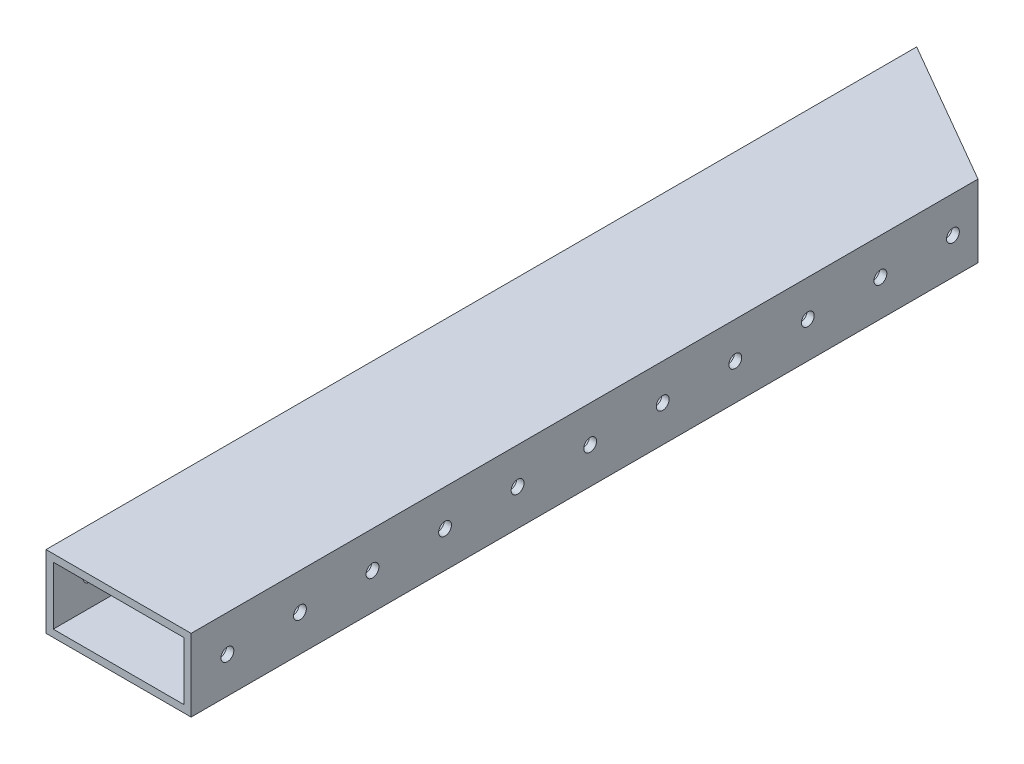
SolidWorks part; units mm, degrees
ref_plane "Front Plane" through (0, 0, 0) normal (0, 0, 1) x (1, 0, 0)
ref_plane "Top Plane" through (0, 0, 0) normal (0, 1, 0) x (1, 0, 0)
ref_plane "Right Plane" through (0, 0, 0) normal (1, 0, 0) x (0, 0, -1)
sketch "Sketch1" plane through (0, 0, 0) normal (0, 0, 1) x (1, 0, 0)
  line L1 (-25.4, -12.7) -> (25.4, -12.7)
  line L2 (-25.4, -12.7) -> (-25.4, 12.7)
  line L3 (-25.4, 12.7) -> (25.4, 12.7)
  line L4 (25.4, -12.7) -> (25.4, 12.7)
  line L5 (-25.4, -12.7) -> (25.4, 12.7) construction
  line L6 (-25.4, 12.7) -> (25.4, -12.7) construction
  line L7 (-22.86, -10.16) -> (22.86, -10.16)
  line L8 (-22.86, -10.16) -> (-22.86, 10.16)
  line L9 (-22.86, 10.16) -> (22.86, 10.16)
  line L10 (22.86, -10.16) -> (22.86, 10.16)
  line L11 (-22.86, -10.16) -> (22.86, 10.16) construction
  line L12 (-22.86, 10.16) -> (22.86, -10.16) construction
  point P0 (0, 0)
  point P6 (0, 0)
  dimension "D1" = 50.8
  dimension "D2" = 25.4
  dimension "D3" = 2.54
  dimension "D4" = 2.54
extrude "Boss-Extrude1" add sketch "Sketch1" against normal blind 533.4
hole_wizard "#8 Clearance Hole1" positions "Sketch2" profile "Sketch3" hole size "#8" standard "ANSI Inch" end condition through all
sketch "Sketch2" plane through (25.4, 0, 0) normal (1, 0, 0) x (0, 0, -1)
  line L0 (533.4, -12.7) -> (0, -12.7) construction
  point P0 (12.7, 0)
  point P16 (38.1, 0)
  point P17 (63.5, 0)
  point P18 (88.9, 0)
  point P19 (114.3, 0)
  point P20 (139.7, 0)
  point P21 (165.1, 0)
  point P22 (190.5, 0)
  point P23 (215.9, 0)
  point P24 (241.3, 0)
  point P25 (266.7, 0)
  point P26 (292.1, 0)
  point P27 (317.5, 0)
  point P28 (342.9, 0)
  point P29 (368.3, 0)
  point P30 (393.7, 0)
  point P31 (419.1, 0)
  point P32 (444.5, 0)
  point P33 (469.9, 0)
  point P34 (495.3, 0)
  point P35 (520.7, 0)
  dimension "D1" = 12.7
  dimension "D2" = 12.7
  dimension "D3" = 21
sketch "Sketch3" plane through (25.4, 0, -12.7) normal (0, 1, 0) x (0, 0, -1)
  line L0 (0, 0) -> (0, 50.8)
  line L1 (0, 50.8) -> (2.2479, 50.8)
  line L2 (2.2479, 50.8) -> (2.2479, 0)
  line L5 (2.2479, 0) -> (0, 0)
  line L11 (0, -6.35) -> (0, 107.95) construction
  dimension "Thru Hole Dia." = 4.4958
  dimension "Thru Hole Depth" = 50.8
sketch "Sketch4" plane through (0, 12.7, 0) normal (0, 1, 0) x (1, 0, 0)
  line L0 (-7.2063, 228.6) -> (135.5131, 228.6)
  line L3 (135.5131, 228.6) -> (135.5131, -17.6414)
  line L4 (135.5131, -17.6414) -> (-94.0569, -17.6414)
  line L5 (-94.0569, -17.6414) -> (-94.0569, 228.6)
  line L6 (-94.0569, 228.6) -> (-7.2063, 228.6)
extrude "Cut-Extrude2" cut sketch "Sketch4" against normal blind 76.962
ref_plane "Plane1" through (-25.4, 12.7, -533.4) normal (0, 0, 1) x (1, 0, 0)
sketch "Sketch6" plane through (0, 12.7, 0) normal (0, 1, 0) x (1, 0, 0)
  line L0 (-25.4, 533.4) -> (25.4, 504.0706)
  line L1 (-109.22, 533.4) -> (58.42, 533.4) construction
  line L2 (-25.4, 533.4) -> (-25.4, 228.6) construction
  line L3 (25.4, 533.4) -> (25.4, 228.6) construction
  line L4 (25.4, 504.0706) -> (25.4, 533.4)
  line L5 (25.4, 533.4) -> (-25.4, 533.4)
  dimension "D1" = 30
extrude "Cut-Extrude4" cut sketch "Sketch6" against normal blind 40.64
